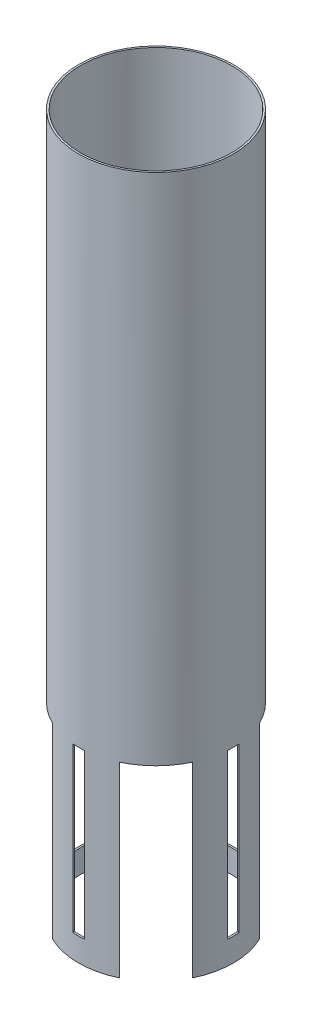
SolidWorks part; units mm, degrees
ref_plane "Front Plane" through (0, 0, 0) normal (0, 0, 1) x (1, 0, 0)
ref_plane "Top Plane" through (0, 0, 0) normal (0, 1, 0) x (1, 0, 0)
ref_plane "Right Plane" through (0, 0, 0) normal (1, 0, 0) x (0, 0, -1)
sketch "Sketch1" plane through (0, 0, 0) normal (0, 1, 0) x (1, 0, 0)
  circle A0 centre (0, 0) radius 33.16
  circle A1 centre (0, 0) radius 32.385
  dimension "D1" = 66.32
  dimension "D2" = 64.77
extrude "Boss-Extrude1" add sketch "Sketch1" along normal mid plane 300
sketch "Sketch2" plane through (0, 0, 0) normal (0, 0, 1) x (1, 0, 0)
  line L0 (-33.16, -150) -> (33.16, -150) construction
  line L1 (-2.5, -140) -> (2.5, -140)
  line L2 (-2.5, -140) -> (-2.5, -70)
  line L3 (-2.5, -70) -> (2.5, -70)
  line L4 (2.5, -140) -> (2.5, -70)
  line L5 (-2.5, -140) -> (2.5, -70) construction
  line L6 (-2.5, -70) -> (2.5, -140) construction
  point P0 (0, -105)
  dimension "D1" = 5
  dimension "D2" = 70
  dimension "D3" = 10
extrude "Cut-Extrude1" cut sketch "Sketch2" against normal through all
pattern_circular "CirPattern1" count 4 over 360 about axis through (0, 0, 0) along (0, 1, 0) of "Cut-Extrude1"
ref_plane "Plane1" through (14.8942, 0, 14.8942) normal (-0.7071, 0, -0.7071) x (-0.7071, 0, 0.7071)
sketch "Sketch3" plane through (14.8942, 0, 14.8942) normal (-0.7071, 0, -0.7071) x (-0.7071, 0, 0.7071)
  line L0 (-33.16, -150) -> (33.16, -150) construction
  line L1 (-11, -70) -> (11, -70)
  line L2 (-11, -70) -> (-11, -150)
  line L3 (-11, -150) -> (11, -150)
  line L4 (11, -70) -> (11, -150)
  line L5 (-11, -70) -> (11, -150) construction
  line L6 (-11, -150) -> (11, -70) construction
  point P0 (0, -110)
  dimension "D1" = 80
  dimension "D2" = 22
extrude "Cut-Extrude2" cut sketch "Sketch3" against normal through all
pattern_circular "CirPattern2" count 4 over 360 about axis through (0, 0, 0) along (0, 1, 0) of "Cut-Extrude2"
